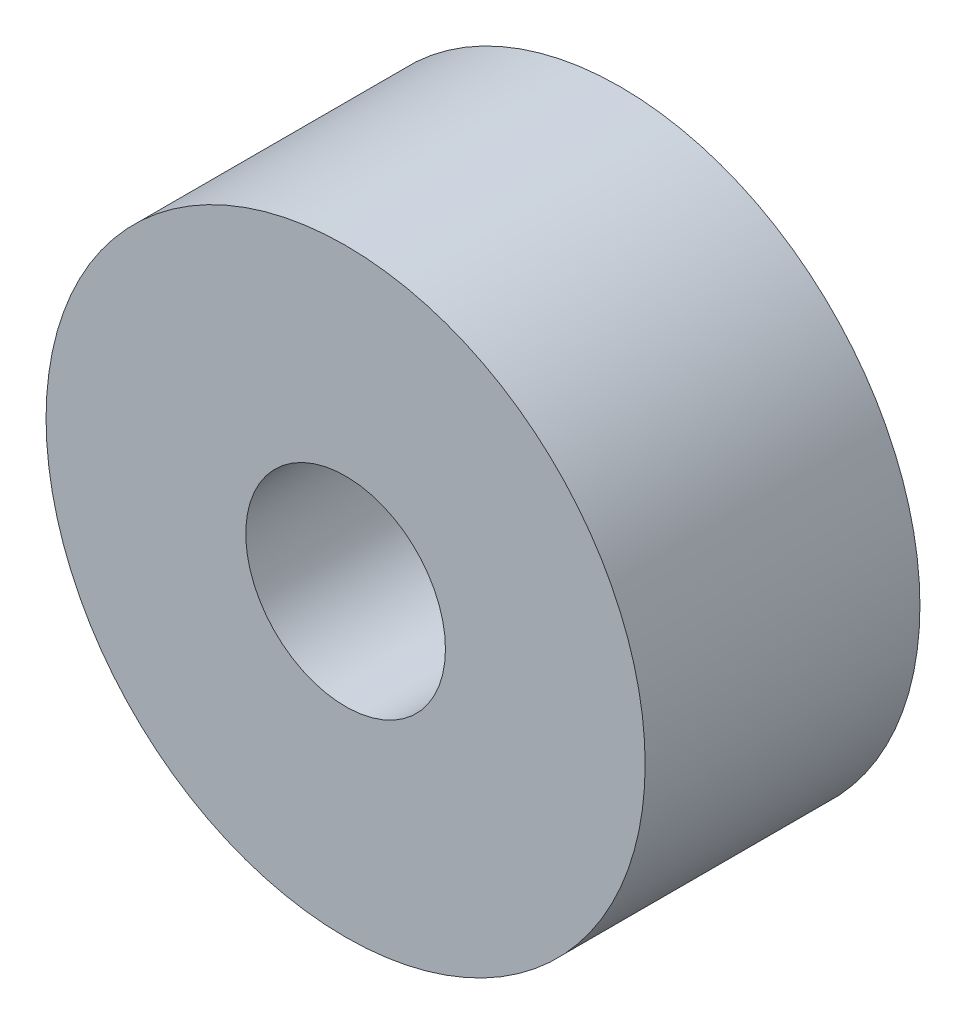
SolidWorks part; units mm, degrees
ref_plane "Front Plane" through (0, 0, 0) normal (0, 0, 1) x (1, 0, 0)
ref_plane "Top Plane" through (0, 0, 0) normal (0, 1, 0) x (1, 0, 0)
ref_plane "Right Plane" through (0, 0, 0) normal (1, 0, 0) x (0, 0, -1)
sketch "Sketch1" plane through (0, 0, 0) normal (0, 0, 1) x (1, 0, 0)
  circle A0 centre (0, 0) radius 7.5
  circle A1 centre (0, 0) radius 2.5
  dimension "D1" = 5
  dimension "D2" = 15
extrude "Boss-Extrude1" add sketch "Sketch1" along normal blind 6.88
